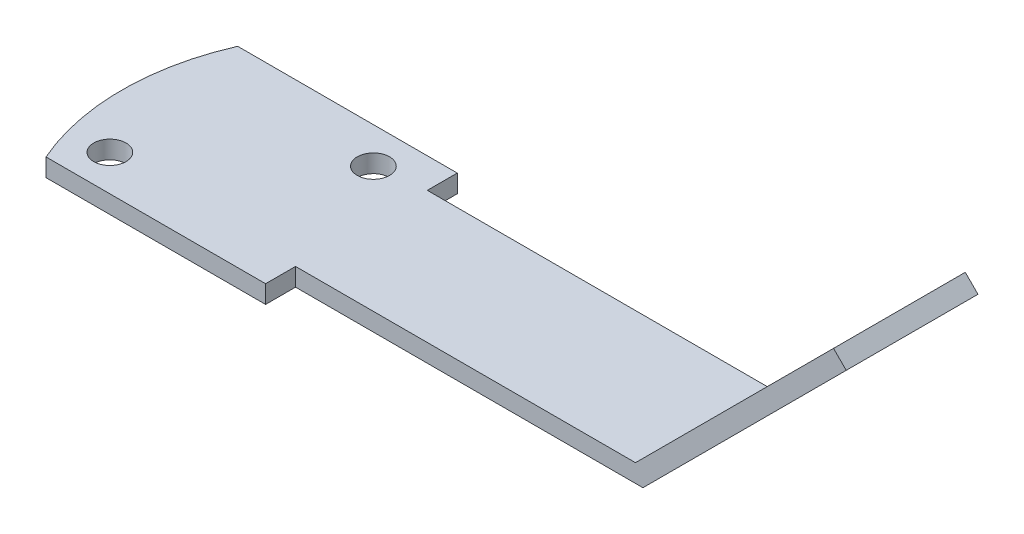
SolidWorks part; units mm, degrees
ref_plane "Front Plane" through (0, 0, 0) normal (0, 0, 1) x (1, 0, 0)
ref_plane "Top Plane" through (0, 0, 0) normal (0, 1, 0) x (1, 0, 0)
ref_plane "Right Plane" through (0, 0, 0) normal (1, 0, 0) x (0, 0, -1)
sketch "Main Body Sketch" plane through (0, 0, 0) normal (0, 1, 0) x (1, 0, 0)
  line L1 (0, 0) -> (-29, 0)
  line L2 (0, 0) -> (0, -11)
  line L3 (0, -11) -> (-29, -11)
  line L4 (-29, 0) -> (-29, -11)
  line L5 (-29, -13.5) -> (-47.3303, -13.5)
  line L6 (-29, -13.5) -> (-29, 2.5)
  line L7 (-29, 2.5) -> (-47.3303, 2.5)
  line L8 (-47.3303, -13.5) -> (-47.3303, 2.5)
  arc A0 (-47.3303, -13.5) -> (-47.3303, 2.5) centre (-29, -5.5) cw
  point P9 (-29, -5.5)
  point P10 (-47.3303, -5.5)
  point P11 (-29, -5.5)
  point P13 (-49, -5.5)
  dimension "D5" = 20
  dimension "D1" = 29
  dimension "D2" = 49
  dimension "D3" = 16
  dimension "D4" = 11
extrude "Main Body Extrude" add sketch "Main Body Sketch" along normal blind 1.5 contours L8 L5 L6 L4 L7 | L1 L4 L3 L2 | A0 L8
sketch "Hole Locations on Main Body" plane through (0, 0, 0) normal (0, 1, 0) x (1, 0, 0)
  line L1 (0, 0) -> (0, -11) construction
  line L2 (-33, -0.5) -> (-45, -0.5) construction
  line L3 (-33, -0.5) -> (-33, -10.5) construction
  line L4 (-33, -10.5) -> (-45, -10.5) construction
  line L5 (-45, -0.5) -> (-45, -10.5) construction
  point P4 (-33, -5.5)
  dimension "D1" = 45
  dimension "D2" = 12
  dimension "D3" = 10
ref_plane "Tilted Plane 135* from Top Plane" through (0, 0, 0) normal (-0.7071, 0.7071, 0) x (0, 0, 1)
sketch "Tilted Offshoot Sketch" plane through (0, 0, 0) normal (-0.7071, 0.7071, 0) x (0, 0, 1)
  line L1 (0, 0) -> (11, 0)
  line L2 (0, 0) -> (0, 24)
  line L3 (0, 24) -> (11, 24)
  line L4 (11, 0) -> (11, 24)
  dimension "D1" = 24
extrude "Tilted Offshoot Extrude" add sketch "Tilted Offshoot Sketch" along normal blind 1.5
sketch "Hole Location On Offshoot" plane through (0, 0, 0) normal (-0.7071, 0.7071, 0) x (0, 0, 1)
  line L0 (0, 24) -> (11, 24) construction
  point P0 (5.5, 20)
  point P3 (5.5, 24)
  dimension "D1" = 4
hole_wizard "Ø2.7 (2.7) Diameter Hole1" positions "Sketch7" profile "Sketch8" hole size "Ø2.7" standard "ANSI Metric" end condition through all
sketch "Sketch7" plane through (0, 1.5, 0) normal (0, 1, 0) x (1, 0, 0)
  point P0 (-45, -10.5)
  point P3 (-33, -0.5)
sketch "Sketch8" plane through (-45, 1.5, 10.5) normal (1, 0, 0) x (0, 0, 1)
  line L0 (0, 0) -> (0, 1.5)
  line L1 (0, 1.5) -> (1.35, 1.5)
  line L2 (1.35, 1.5) -> (1.35, 0)
  line L5 (1.35, 0) -> (0, 0)
  line L11 (0, -6.35) -> (0, 107.95) construction
  dimension "Thru Hole Dia." = 2.7
  dimension "Thru Hole Depth" = 1.5
hole_wizard "Ø3.0 (3) Diameter Hole1" positions "Sketch9" profile "Sketch10" hole size "Ø3.0" standard "ANSI Metric" end condition through all
sketch "Sketch9" plane through (-1.0607, 1.0607, 0) normal (-0.7071, 0.7071, 0) x (0.7071, 0.7071, 0)
  point P0 (20, -5.5)
sketch "Sketch10" plane through (13.0815, 15.2028, 5.5) normal (0, 0, 1) x (-0.7071, -0.7071, 0)
  line L0 (0, 0) -> (0, 13.5)
  line L1 (0, 13.5) -> (1.5, 13.5)
  line L2 (1.5, 13.5) -> (1.5, 0)
  line L5 (1.5, 0) -> (0, 0)
  line L11 (0, -6.35) -> (0, 107.95) construction
  dimension "Thru Hole Dia." = 3
  dimension "Thru Hole Depth" = 13.5
hole_wizard "Ø2.7 (2.7) Diameter Hole2" positions "Sketch11" profile "Sketch12" hole size "Ø2.7" standard "ANSI Metric"
sketch "Sketch11" plane through (0, 1.5, 0) normal (0, 1, 0) x (1, 0, 0)
  point P0 (-33, -10.5)
  point P3 (-45, -0.5)
sketch "Sketch12" plane through (-33, 1.5, 10.5) normal (1, 0, 0) x (0, 0, 1)
  line L0 (0, 0) -> (0, 1.5)
  line L1 (0, 1.5) -> (1.35, 1.5)
  line L2 (1.35, 1.5) -> (1.35, 0)
  line L5 (1.35, 0) -> (0, 0)
  line L11 (0, -6.35) -> (0, 107.95) construction
  dimension "Thru Hole Dia." = 2.7
  dimension "Thru Hole Depth" = 1.5
